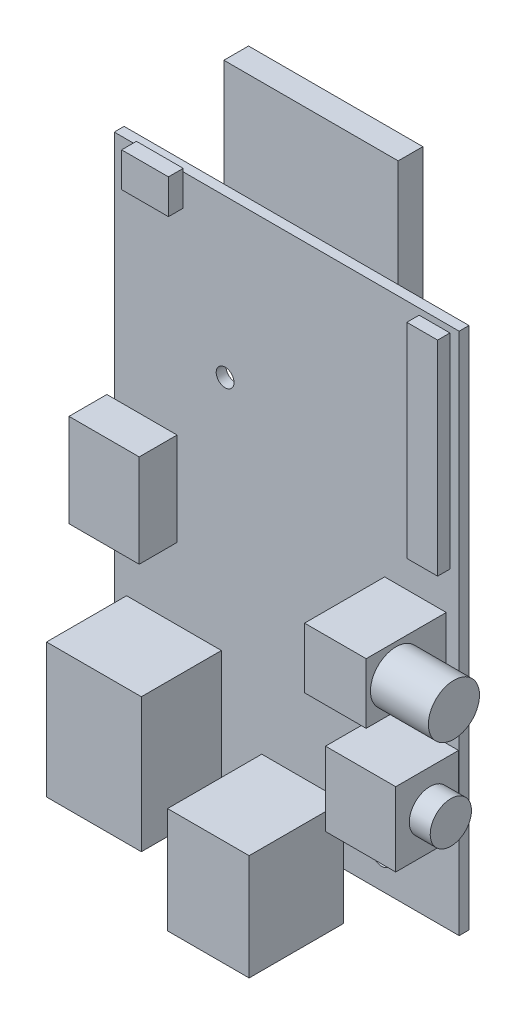
SolidWorks part; units mm, degrees
ref_plane "Alzado" through (0, 0, 0) normal (0, 0, 1) x (1, 0, 0)
ref_plane "Planta" through (0, 0, 0) normal (0, 1, 0) x (1, 0, 0)
ref_plane "Vista lateral" through (0, 0, 0) normal (1, 0, 0) x (0, 0, -1)
sketch "Croquis1" plane through (0, 0, 0) normal (0, 0, 1) x (1, 0, 0)
  line L1 (0, 0) -> (56, 0)
  line L2 (0, 0) -> (0, 85)
  line L3 (0, 85) -> (56, 85)
  line L4 (56, 0) -> (56, 85)
  circle A0 centre (43.4, 4.9) radius 1.45
  circle A1 centre (18, 59.5) radius 1.45
  dimension "D5" = 2.9
  dimension "D6" = 18
  dimension "D1" = 85
  dimension "D2" = 56
  dimension "D3" = 4.9
  dimension "D4" = 12.6
  dimension "D7" = 25.5
extrude "Saliente-Extruir1" add sketch "Croquis1" along normal blind 1.6
sketch "Croquis2" plane through (0, 0, 1.6) normal (0, 0, 1) x (1, 0, 0)
  line L0 (56, 85) -> (0, 85) construction
  line L1 (3.6, 79.9) -> (11.2, 79.9)
  line L2 (3.6, 79.9) -> (3.6, 85.5)
  line L3 (3.6, 85.5) -> (11.2, 85.5)
  line L4 (11.2, 79.9) -> (11.2, 85.5)
  line L5 (0, 85) -> (0, 0) construction
  dimension "D1" = 0.5
  dimension "D2" = 3.6
  dimension "D3" = 7.6
  dimension "D4" = 5.6
extrude "Saliente-Extruir2" add sketch "Croquis2" along normal blind 2.4
sketch "Croquis3" plane through (0, 0, 1.6) normal (0, 0, 1) x (1, 0, 0)
  line L0 (3.6, 85) -> (0, 85) construction
  line L1 (-1.2, 47.5) -> (10.2, 47.5)
  line L2 (-1.2, 47.5) -> (-1.2, 32.4)
  line L3 (-1.2, 32.4) -> (10.2, 32.4)
  line L4 (10.2, 47.5) -> (10.2, 32.4)
  line L5 (0, 85) -> (0, 0) construction
  dimension "D1" = 37.5
  dimension "D2" = 1.2
  dimension "D3" = 15.1
  dimension "D4" = 11.4
extrude "Saliente-Extruir3" add sketch "Croquis3" along normal blind 6.15
sketch "Croquis4" plane through (0, 0, 1.6) normal (0, 0, 1) x (1, 0, 0)
  line L0 (0, 0) -> (56, 0) construction
  line L1 (2, -1) -> (17.4, -1)
  line L2 (2, -1) -> (2, 20.8)
  line L3 (2, 20.8) -> (17.4, 20.8)
  line L4 (17.4, -1) -> (17.4, 20.8)
  line L5 (0, 32.4) -> (0, 0) construction
  dimension "D1" = 1
  dimension "D2" = 2
  dimension "D3" = 21.8
  dimension "D4" = 15.4
extrude "Saliente-Extruir4" add sketch "Croquis4" along normal blind 13
sketch "Croquis5" plane through (0, 0, 1.6) normal (0, 0, 1) x (1, 0, 0)
  line L0 (17.4, 0) -> (56, 0) construction
  line L1 (23.95, -7.7) -> (37.2, -7.7)
  line L2 (23.95, -7.7) -> (23.95, 9.5)
  line L3 (23.95, 9.5) -> (37.2, 9.5)
  line L4 (37.2, -7.7) -> (37.2, 9.5)
  line L5 (56, 0) -> (56, 85) construction
  dimension "D1" = 7.7
  dimension "D2" = 18.8
  dimension "D3" = 13.25
  dimension "D4" = 17.2
extrude "Saliente-Extruir5" add sketch "Croquis5" along normal blind 15.3
sketch "Croquis6" plane through (0, 0, 1.6) normal (0, 0, 1) x (1, 0, 0)
  line L1 (55.9, 14) -> (44.5, 14)
  line L2 (55.9, 14) -> (55.9, 26)
  line L3 (55.9, 26) -> (44.5, 26)
  line L4 (44.5, 14) -> (44.5, 26)
  line L5 (37.2, 0) -> (56, 0) construction
  line L6 (56, 0) -> (56, 85) construction
  dimension "D1" = 14
  dimension "D2" = 11.4
  dimension "D3" = 12
  dimension "D4" = 0.1
extrude "Saliente-Extruir6" add sketch "Croquis6" along normal blind 10.2
sketch "Croquis7" plane through (0, 0, 1.6) normal (0, 0, 1) x (1, 0, 0)
  line L0 (56, 0) -> (56, 85) construction
  line L1 (53.9, 44.4) -> (43.9, 44.4)
  line L2 (53.9, 44.4) -> (53.9, 34.6)
  line L3 (53.9, 34.6) -> (43.9, 34.6)
  line L4 (43.9, 44.4) -> (43.9, 34.6)
  line L5 (56, 85) -> (11.2, 85) construction
  dimension "D1" = 2.1
  dimension "D2" = 10
  dimension "D3" = 9.8
  dimension "D4" = 40.6
extrude "Saliente-Extruir7" add sketch "Croquis7" along normal blind 13
sketch "Croquis8" plane through (0, 0, 1.6) normal (0, 0, 1) x (1, 0, 0)
  line L0 (56, 0) -> (56, 85) construction
  line L1 (54.5, 84) -> (49.5, 84)
  line L2 (54.5, 84) -> (54.5, 50.8)
  line L3 (54.5, 50.8) -> (49.5, 50.8)
  line L4 (49.5, 84) -> (49.5, 50.8)
  line L5 (56, 85) -> (11.2, 85) construction
  dimension "D1" = 5
  dimension "D2" = 33.2
  dimension "D3" = 1.5
  dimension "D4" = 1
extrude "Saliente-Extruir8" add sketch "Croquis8" along normal blind 2
sketch "Croquis10" plane through (0, 0, 0) normal (0, 0, -1) x (-1, 0, 0)
  line L0 (-56, 85) -> (0, 85) construction
  line L1 (-44.5, 67.3) -> (-16.2, 67.3)
  line L2 (-44.5, 67.3) -> (-44.5, 102.4)
  line L3 (-44.5, 102.4) -> (-16.2, 102.4)
  line L4 (-16.2, 67.3) -> (-16.2, 102.4)
  line L5 (-56, 0) -> (-56, 85) construction
  line L6 (-56, 85) -> (-11.2, 85) construction
  dimension "D1" = 17.7
  dimension "D2" = 28.3
  dimension "D3" = 11.5
  dimension "D4" = 17.4
extrude "Saliente-Extruir9" add sketch "Croquis10" along normal blind 4
sketch "Croquis11" plane through (56, 0, 0) normal (1, 0, 0) x (0, 0, -1)
  line L0 (-11.8, 20) -> (-3, 20) construction
  line L1 (-11.8, 14) -> (-11.8, 26) construction
  line L2 (-3, 20) -> (0, 20) construction
  line L3 (0, 0) -> (0, 85) construction
  circle A0 centre (-6.35, 20) radius 3.35
  dimension "D2" = 6.7
  dimension "D1" = 3
extrude "Saliente-Extruir10" add sketch "Croquis11" along normal blind 3.4
sketch "Croquis12" plane through (53.9, 0, 0) normal (1, 0, 0) x (0, 0, -1)
  line L0 (-14.6, 39.5) -> (-1.6, 39.5) construction
  line L1 (-14.6, 34.6) -> (-14.6, 44.4) construction
  line L2 (-1.6, 34.6) -> (-1.6, 44.4) construction
  circle A0 centre (-9.75, 39.5) radius 4.15
  point P6 (-5.6, 39.5)
  dimension "D2" = 8.3
  dimension "D1" = 4
extrude "Saliente-Extruir11" add sketch "Croquis12" along normal blind 9.4
